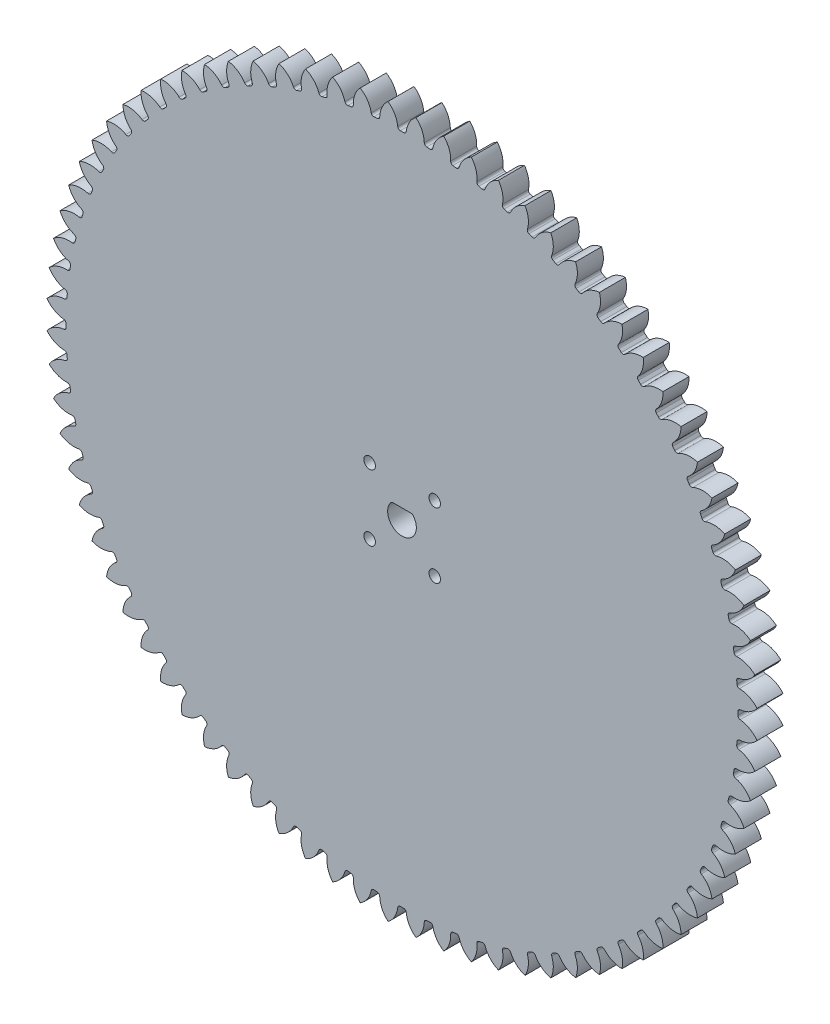
SolidWorks part; units mm, degrees
ref_plane "Front Plane" through (0, 0, 0) normal (0, 0, 1) x (1, 0, 0)
ref_plane "Top Plane" through (0, 0, 0) normal (0, 1, 0) x (1, 0, 0)
ref_plane "Right Plane" through (0, 0, 0) normal (1, 0, 0) x (0, 0, -1)
sketch "Sketch1" plane through (0, 0, 0) normal (0, 0, 1) x (1, 0, 0)
  circle A0 centre (0, 0) radius 120
  circle A1 centre (0, 0) radius 123
  dimension "D1" = 240
  dimension "D2" = 246
extrude "Boss-Extrude1" add sketch "Sketch1" along normal blind 9 contours A1 A0
sketch "Sketch2" plane through (0, 0, 9) normal (0, 0, 1) x (1, 0, 0)
  line L0 (0, 123) -> (0, 0) construction
  line L1 (0, 0) -> (9.6505, 122.6208) construction
  line L2 (0, 0) -> (4.829, 122.9052) construction
  line L3 (-1.4269, 116.2412) -> (0, 0) construction
  line L4 (-2.356, 119.9769) -> (2.356, 119.9769) construction
  line L5 (2.356, 119.9769) -> (7.0645, 119.7919) construction
  line L6 (-3.3685, 122.9539) -> (0, 113.6989) construction
  circle A0 centre (0, 0) radius 117 construction
  circle A2 centre (0, 0) radius 123 construction
  arc A3 (-4.856, 122.9041) -> (-1.4269, 116.2412) centre (-9.8145, 116.1383) cw
  circle A4 centre (0, 0) radius 123 construction
  arc A5 (4.856, 122.9041) -> (1.4269, 116.2412) centre (9.8145, 116.1383) ccw
  circle A6 centre (0, 0) radius 120 construction
  arc A7 (1.4269, 116.2412) -> (-1.4269, 116.2412) centre (0, 0) ccw
  circle M1 centre (0, 0) radius 123
  dimension "D1" = 4.5
  dimension "D2" = 6
  dimension "D4" = 20
  dimension "D3" = 0.75
extrude "Cut-Extrude1" cut sketch "Sketch2" against normal through all both and the other way through all contours A7 A5 A3 M1
fillet "Fillet1" radius 0.9 2 edges at (1.4269, 116.2412, 4.5) (-1.4269, 116.2412, 4.5)
pattern_circular "CirPattern3" count 80 over 360 about axis through (0, 0, 0) along (0, 0, 1) of "Fillet1", "Cut-Extrude1"
sketch "Sketch3" plane through (0, 0, 9) normal (0, 0, 1) x (1, 0, 0)
  line L0 (-3.5602, 3.475) -> (3.5602, 3.475)
  arc A0 (-3.5602, 3.475) -> (3.5602, 3.475) centre (0, 0) ccw
  point P3 (0, 4.975)
  dimension "D1" = 9.95
  dimension "D2" = 1.5
extrude "Cut-Extrude2" cut sketch "Sketch3" against normal through all
fillet "Fillet2" radius 1 2 edges at (-3.5602, 3.475, 4.5) (3.5602, 3.475, 4.5)
sketch "Sketch4" plane through (0, 0, 9) normal (0, 0, 1) x (1, 0, 0)
  line L0 (0, 0) -> (116.25, 0) construction
  line L1 (0, 0) -> (0.5769, 116.2486) construction
  line L2 (82.2012, 82.2012) -> (0, 0) construction
  arc A0 (116.2486, -0.5769) -> (116.2486, 0.5769) centre (0, 0) ccw construction
  circle A1 centre (0, 0) radius 116.25
  circle A2 centre (11.3137, 11.3137) radius 2
  circle A3 centre (-11.2009, 11.4254) radius 2
  circle A4 centre (-11.2009, -11.4254) radius 2
  circle A5 centre (11.3137, -11.3137) radius 2
  point P9 (82.2012, 82.2012)
  dimension "D3" = 4
  dimension "D1" = 45
  dimension "D2" = 16
extrude "Cut-Extrude3" cut sketch "Sketch4" against normal through all contours A3 | A5 | A4 | A2
equation "\"Module\"= 3mm"
equation "\"No. Teeth\"= 80"
equation "\"Contact Angle\"= 20"
equation "\"D1@Sketch1\"=\"Module\" * \"No. Teeth\""
equation "\"D2@Sketch1\"=(\"No. Teeth\" + 2) * \"Module\""
equation "\"D1@Sketch2\"=360/\"No. Teeth\""
equation "\"D2@Sketch2\"=2*\"Module\""
equation "\"D4@Sketch2\"=\"Contact Angle\""
equation "\"D1@Fillet1\"=0.3 * \"Module\""
equation "\"D1@CirPattern3\"=\"No. Teeth\""
